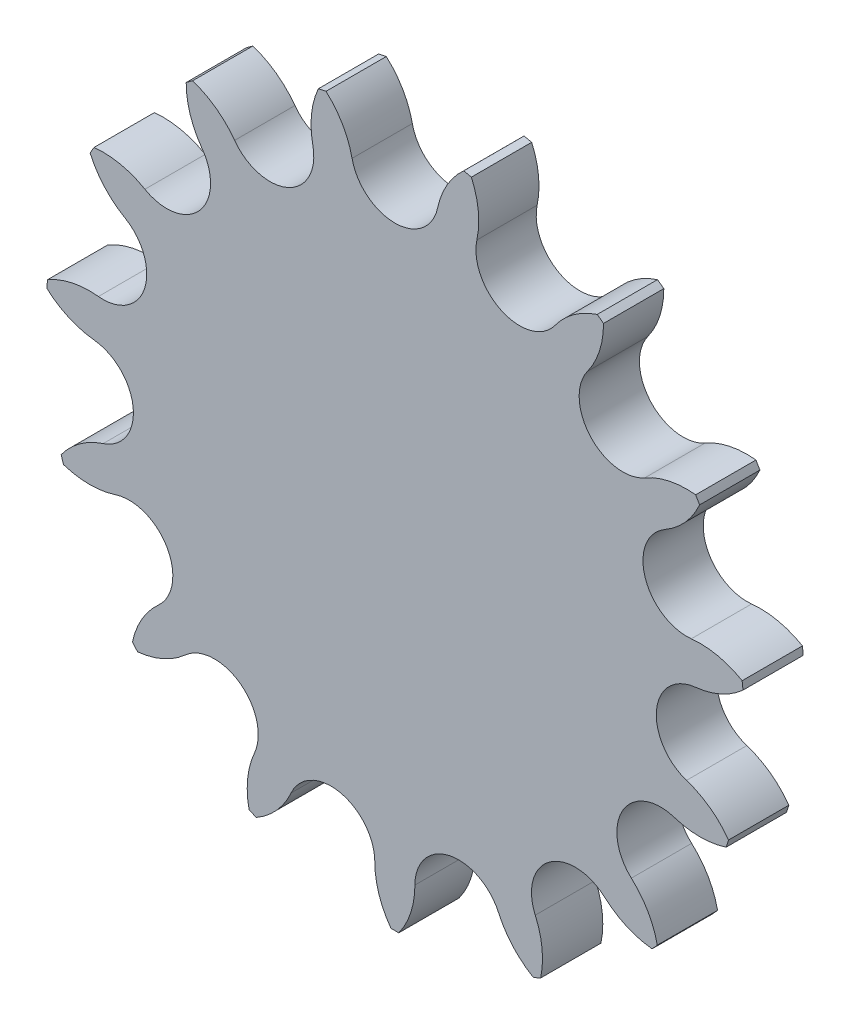
SolidWorks part; units mm, degrees
material "AISI 1020"
ref_plane "Спереди" through (0, 0, 0) normal (0, 0, 1) x (1, 0, 0)
ref_plane "Сверху" through (0, 0, 0) normal (0, 1, 0) x (1, 0, 0)
ref_plane "Справа" through (0, 0, 0) normal (1, 0, 0) x (0, 0, -1)
sketch "Эскиз1" plane through (0, 0, 0) normal (0, 0, 1) x (1, 0, 0)
  line L4 (0, 0) -> (0, 30.5418)
  line L5 (0, 30.5418) -> (12.4225, 27.9013)
  line L6 (12.4225, 27.9013) -> (0, 0)
  circle A1 centre (0, 30.5418) radius 4.255
  circle A2 centre (12.4225, 27.9013) radius 4.255
  circle A3 centre (0, 0) radius 34.7968 construction
  dimension "D6" = 8.51
  dimension "D1" = 69.5936
  dimension "D5" = 24
  dimension "D7" = 12.7
sketch "Эскиз2" plane through (0, 0, 0) normal (0, 0, 1) x (1, 0, 0)
  line L0 (0, 0) -> (0, 26.1868)
  line L1 (0, 0) -> (10.6511, 23.9228)
  line L4 (12.4225, 27.9013) -> (0, 0) construction
  arc A0 (8.1626, 28.8068) -> (7.6159, 33.9532) centre (0, 30.5418) ccw
  arc A1 (0, 34.7968) -> (14.1531, 31.7885) centre (0, 0) cw construction
  circle A2 centre (0, 30.5418) radius 4.255 construction
  circle A3 centre (12.4225, 27.9013) radius 4.255 construction
  circle A5 centre (0, 30.5418) radius 4.355
  arc A6 (0, 26.1868) -> (4.2598, 29.6364) centre (0, 30.5418) ccw
  arc A7 (6.8525, 34.1154) -> (4.2598, 29.6364) centre (12.4225, 27.9013) ccw
  circle A8 centre (12.4225, 27.9013) radius 4.355
  arc A9 (8.1626, 28.8068) -> (10.6511, 23.9228) centre (12.4225, 27.9013) ccw
  arc A10 (6.8525, 34.1154) -> (7.6159, 33.9532) centre (0, 0) cw
  point P6 (0, 0)
  dimension "D1" = 0.1
  dimension "D2" = 0.1
extrude "Бобышка-Вытянуть1" add sketch "Эскиз2" along normal blind 6
pattern_circular "Круговой массив1" count 15 over 360 about axis through (0, 0, 0) along (0, 0, 1) of "Бобышка-Вытянуть1"
sketch "Эскиз3" plane through (0, 0, 6) normal (0, 0, 1) x (1, 0, 0)
  line L0 (0, 0) -> (0, 30) construction
  line L1 (0, 0) -> (25.9808, 15) construction
  circle A0 centre (0, 0) radius 17.5
  circle A1 centre (0, 0) radius 30 construction
  circle A2 centre (0, 30) radius 4
  circle A3 centre (25.9808, 15) radius 4
  circle A4 centre (25.9808, -15) radius 4
  circle A5 centre (0, -30) radius 4
  circle A6 centre (-25.9808, -15) radius 4
  circle A7 centre (-25.9808, 15) radius 4
  dimension "D1" = 35
  dimension "D2" = 60
  dimension "D3" = 8
  dimension "D5" = 60
  dimension "D6" = 30
  dimension "D4" = 6
extrude "Вырез-Вытянуть1" [suppressed] cut sketch "Эскиз3" against normal through all
equation "\"D5@Эскиз1\"=360/\"_kol-vo\""
equation "\"_kol-vo\"= 15"
equation "\"_Pitch\"=12.7"
equation "\"_d1_max\"= 8.51"
equation "\"_d1_min\"= 7.75"
equation "\"_d2_max\"= 4.45"
equation "\"_T_max\"= 1.6"
equation "\"_h2\"= 11.8"
equation "\"_L_max\"= 16.85"
equation "\"_Lc_max\"= 18.1"
equation "\"D6@Эскиз1\"=\"_d1_max\""
equation "\"D1@Круговой массив1\"=\"_kol-vo\""
equation "\"D7@Эскиз1\"=\"_Pitch\""
